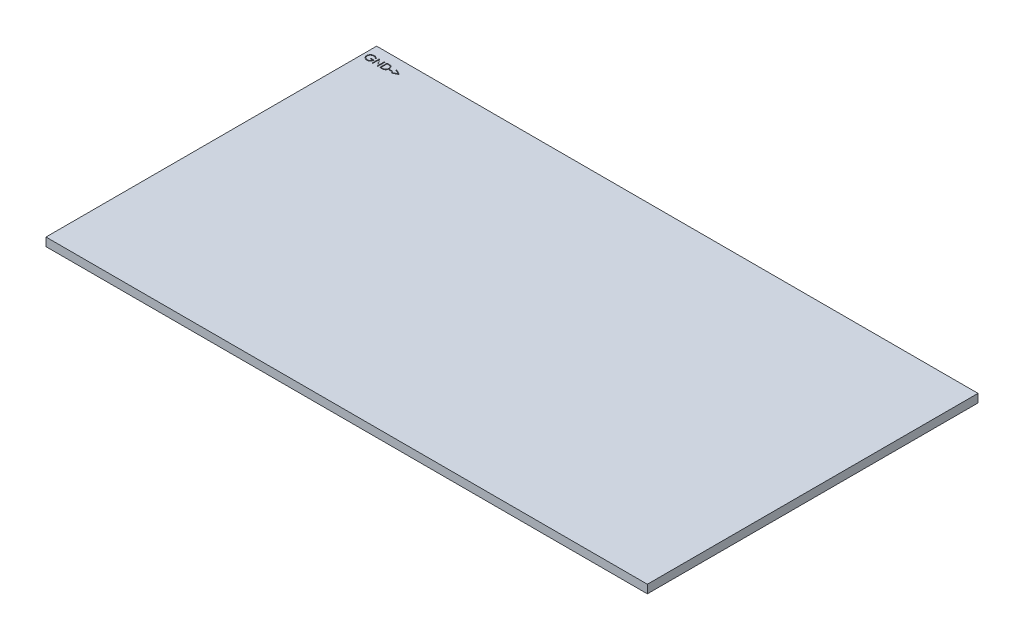
SolidWorks part; units mm, degrees
ref_plane "Front Plane" through (0, 0, 0) normal (0, 0, 1) x (1, 0, 0)
ref_plane "Top Plane" through (0, 0, 0) normal (0, 1, 0) x (1, 0, 0)
ref_plane "Right Plane" through (0, 0, 0) normal (1, 0, 0) x (0, 0, -1)
sketch "Sketch1" plane through (0, 0, 0) normal (0, 1, 0) x (1, 0, 0)
  line L1 (0, -13) -> (114.2, -13)
  line L2 (0, -13) -> (0, 49.784)
  line L3 (0, 49.784) -> (114.2, 49.784)
  line L4 (114.2, -13) -> (114.2, 49.784)
  point P7 (6.858, 47.244)
extrude "Boss-Extrude1" add sketch "Sketch1" along normal blind 1.5875
sketch "Sketch2" plane through (0, 1.5875, 0) normal (0, 1, 0) x (1, 0, 0)
  text T0 "GND->" font "Century Gothic" height 1.4
  point P1 (6.858, 47.244)
extrude "Cut-Extrude1" cut sketch "Sketch2" against normal blind 0.2
sketch "Sketch5" plane through (0, 0, 0) normal (0, -1, 0) x (1, 0, 0)
  line L0 (101.1416, -7.6744) -> (94.742, -7.6744) construction
  text T2 "GND->" font "Century Gothic" height 1.4
  point P6 (0, 0)
  point P7 (94.742, -8.382)
extrude "Cut-Extrude2" cut sketch "Sketch5" against normal blind 0.2
